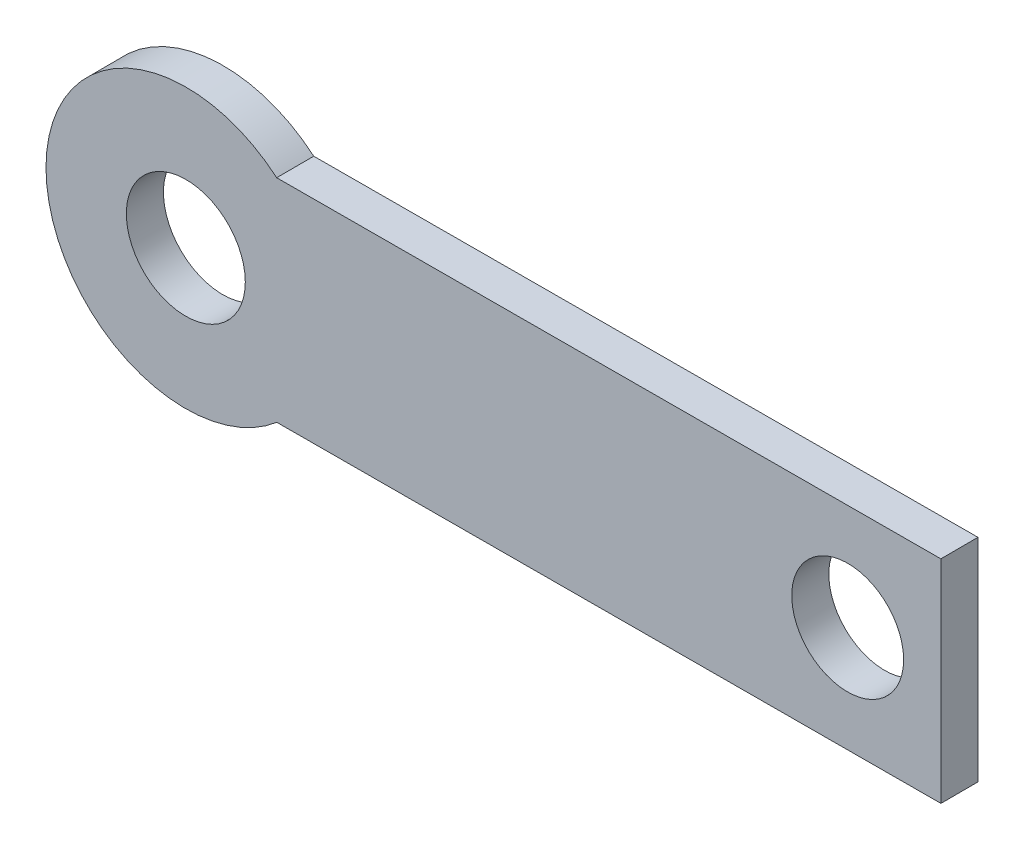
SolidWorks part; units mm, degrees
material "6061-T4 (SS)"
ref_plane "Front Plane" through (0, 0, 0) normal (0, 0, 1) x (1, 0, 0)
ref_plane "Top Plane" through (0, 0, 0) normal (0, 1, 0) x (1, 0, 0)
ref_plane "Right Plane" through (0, 0, 0) normal (1, 0, 0) x (0, 0, -1)
sketch "Sketch1" plane through (0.277, -0.0304, 89.9174) normal (0.0031, -0.0003, 1) x (1, 0, -0.0031)
  line L0 (34.9134, -34.7517) -> (26.9134, -34.7531) construction
  line L1 (-10.0866, -34.7599) -> (34.9134, -34.7517) construction
  line L2 (26.9134, -34.7531) -> (26.9134, -20.7531) construction
  line L3 (29.3511, -23.6027) -> (47.1634, -23.6027)
  line L4 (47.1634, -23.6027) -> (47.1634, -17.9036)
  line L5 (47.1634, -17.9036) -> (29.3511, -17.9036)
  line L6 (28.5084, -20.7531) -> (44.6634, -20.7531) construction
  arc A2 (29.3511, -23.6027) -> (29.3511, -17.9036) centre (26.9134, -20.7531) cw
  circle A3 centre (26.9134, -20.7531) radius 1.595
  circle A4 centre (44.6634, -20.7531) radius 1.5
  point P7 (29.3511, -23.6027)
  point P8 (29.3511, -17.9036)
  point P16 (47.1634, -20.7531)
  dimension "D3" = 17.75
  dimension "D4" = 3.19
  dimension "D7" = 3
  dimension "D8" = 3.75
  dimension "D1" = 8
  dimension "D2" = 14
  dimension "D5" = 20.25
extrude "Boss-Extrude1" add sketch "Sketch1" along normal blind 1
